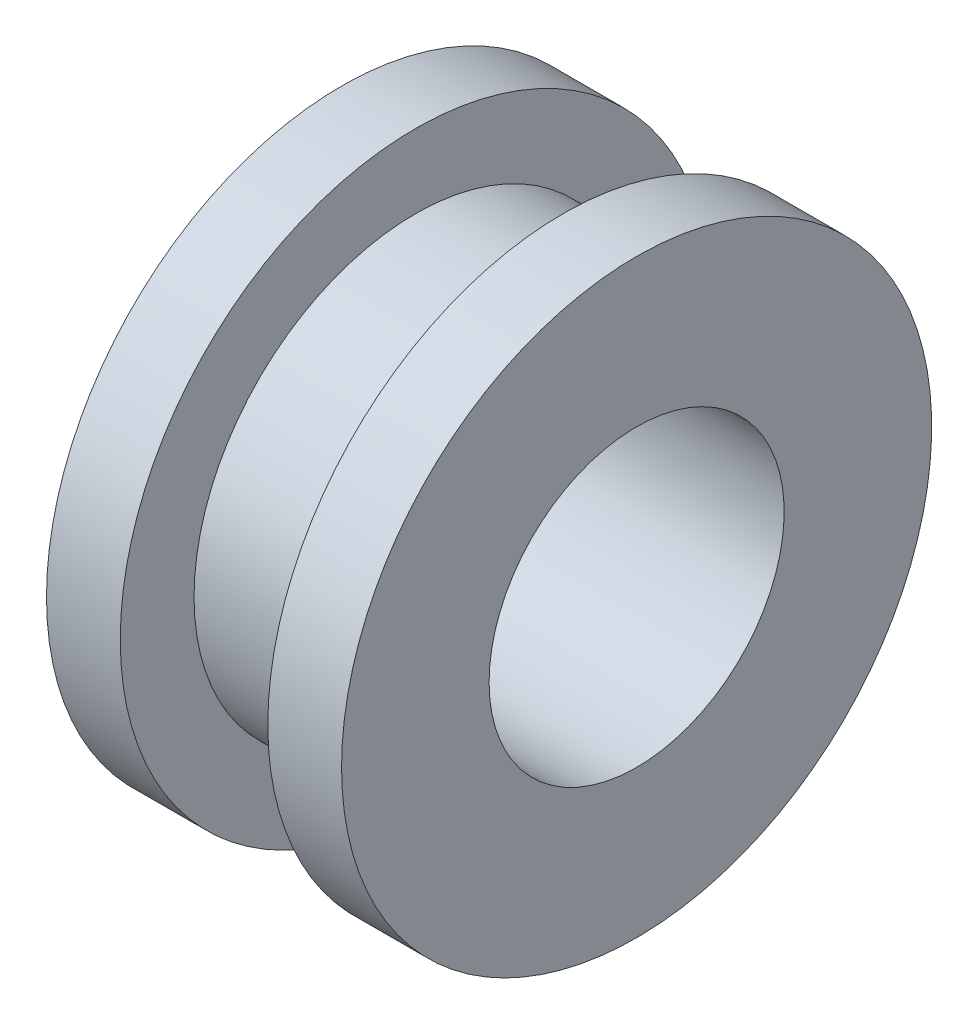
SolidWorks part; units mm, degrees
ref_plane "Plan de face" through (0, 0, 0) normal (0, 0, 1) x (1, 0, 0)
ref_plane "Plan de dessus" through (0, 0, 0) normal (0, 1, 0) x (1, 0, 0)
ref_plane "Plan de droite" through (0, 0, 0) normal (1, 0, 0) x (0, 0, -1)
sketch "Esquisse1" plane through (0, 0, 0) normal (0, 0, 1) x (1, 0, 0)
  line L0 (-1.3499, 0) -> (1.2532, 0) construction
  line L1 (-0.5, 1.5) -> (0.5, 1.5)
  line L2 (0.5, 1.5) -> (0.5, 2)
  line L3 (0.5, 2) -> (1, 2)
  line L4 (1, 2) -> (1, 1)
  line L5 (1, 1) -> (-1, 1)
  line L6 (0, 0) -> (0, 1.4733) construction
  line L7 (-1, 2) -> (-1, 1)
  line L8 (-0.5, 2) -> (-1, 2)
  line L9 (-0.5, 1.5) -> (-0.5, 2)
  point P12 (0, 1)
  point P15 (0, 1.5)
  dimension "D1" = 1
  dimension "D2" = 2
  dimension "D3" = 3
  dimension "D4" = 4
  dimension "D5" = 0.5
revolve "Révolution1" add sketch "Esquisse1" angle 360 about L0
